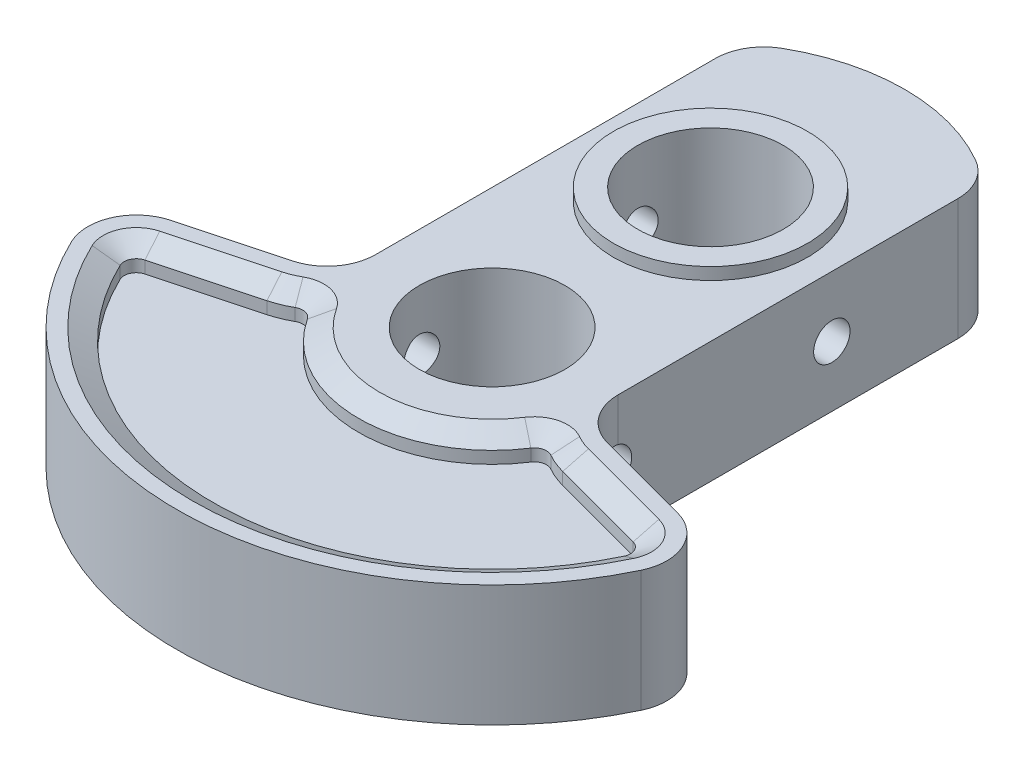
SolidWorks part; units mm, degrees
ref_plane "Front Plane" through (0, 0, 0) normal (0, 0, 1) x (1, 0, 0)
ref_plane "Top Plane" through (0, 0, 0) normal (0, 1, 0) x (1, 0, 0)
ref_plane "Right Plane" through (0, 0, 0) normal (1, 0, 0) x (0, 0, -1)
sketch "Sketch1" plane through (0, 0, 0) normal (0, 1, 0) x (1, 0, 0)
  line L0 (0, 34) -> (0, -26) construction
  line L1 (-10, 30.49) -> (-10, -2.6795)
  line L2 (10, 30.49) -> (10, -2.6795)
  line L3 (-10, 34) -> (-10, -40.4767) construction
  line L4 (10, 34) -> (10, -40.4767) construction
  line L5 (0, 0) -> (-25.1141, -6.7293) construction
  line L6 (0, 0) -> (25.1141, -6.7293) construction
  line L7 (0, 34) -> (0, -40.4767) construction
  line L8 (10, -2.6795) -> (25.1141, -6.7293)
  line L9 (-10, -2.6795) -> (-25.1141, -6.7293)
  arc A0 (10, 30.49) -> (-10, 30.49) centre (0, 18) ccw
  arc A2 (-25.1141, -6.7293) -> (25.1141, -6.7293) centre (0, 0) ccw
  dimension "D2" = 32
  dimension "D5" = 26
  dimension "D1" = 18
  dimension "D6" = 75
  dimension "D7" = 75
  dimension "D3" = 10
  dimension "D4" = 10
extrude "Boss-Extrude1" add sketch "Sketch1" along normal mid plane 10
fillet "Fillet1" radius 4 6 edges at (25.1141, 0, 6.7293) (10, 0, 2.6795) (-25.1141, 0, 6.7293) (-10, 0, 2.6795) (-10, 0, -30.49) (10, 0, -30.49)
sketch "Sketch2" plane through (0, -5, 0) normal (0, -1, 0) x (1, 0, 0)
  circle A0 centre (0, 0) radius 8
  dimension "D1" = 16
extrude "Boss-Extrude2" add sketch "Sketch2" along normal blind 1
sketch "Sketch3" plane through (0, 5, 0) normal (0, 1, 0) x (1, 0, 0)
  circle A0 centre (0, 18) radius 8
  dimension "D1" = 16
  dimension "D2" = 18
extrude "Boss-Extrude3" add sketch "Sketch3" along normal blind 1
sketch "Sketch4" plane through (0, -6, 0) normal (0, -1, 0) x (1, 0, 0)
  circle A0 centre (0, 0) radius 6
  circle A1 centre (0, -18) radius 6
  circle A3 centre (0, -18) radius 8 construction
  dimension "D1" = 12
  dimension "D2" = 12
extrude "Cut-Extrude1" cut sketch "Sketch4" against normal through all
sketch "Sketch5" plane through (0, 5, 0) normal (0, 1, 0) x (1, 0, 0)
  line L20 (12.1883, -6.3717) -> (20.1197, -8.4969)
  line L21 (-20.1197, -8.4969) -> (-12.1883, -6.3717)
  line L22 (12.1883, -6.3717) -> (20.1197, -8.4969)
  line L23 (-20.1197, -8.4969) -> (-12.1883, -6.3717)
  arc A1 (23.472, -11.1833) -> (20.8962, -5.5991) centre (19.8609, -9.4628) ccw construction
  arc A39 (-9.2082, -6.0173) -> (9.2082, -6.0173) centre (0, 0) ccw
  arc A40 (9.2082, -6.0173) -> (10.5397, -5.6951) centre (10.0453, -6.5644) cw
  arc A41 (-9.2082, -6.0173) -> (-10.5397, -5.6951) centre (-10.0453, -6.5644) ccw
  arc A44 (7, 0.3898) -> (12.1883, -6.3717) centre (14, 0.3898) ccw
  arc A45 (20.7637, -9.8929) -> (20.1197, -8.4969) centre (19.8609, -9.4628) ccw
  arc A46 (-20.7637, -9.8929) -> (20.7637, -9.8929) centre (0, 0) ccw
  arc A47 (-20.1197, -8.4969) -> (-20.7637, -9.8929) centre (-19.8609, -9.4628) ccw
  arc A48 (-12.1883, -6.3717) -> (-7, 0.3898) centre (-14, 0.3898) ccw
  arc A49 (10.5397, -5.6951) -> (12.1883, -6.3717) centre (14, 0.3898) ccw
  arc A50 (20.7637, -9.8929) -> (20.1197, -8.4969) centre (19.8609, -9.4628) ccw
  arc A51 (-20.7637, -9.8929) -> (20.7637, -9.8929) centre (0, 0) ccw
  arc A52 (-20.1197, -8.4969) -> (-20.7637, -9.8929) centre (-19.8609, -9.4628) ccw
  arc A53 (-12.1883, -6.3717) -> (-10.5397, -5.6951) centre (-14, 0.3898) ccw
  point P46 (23.4931, -7.7874)
  dimension "D2" = 22
  dimension "D3" = 1
  dimension "D1" = 3
extrude "Cut-Extrude2" cut sketch "Sketch5" against normal blind 2
chamfer "Chamfer1" distance 1 angle 60 10 edges at (11.3424, 5, 6.0861) (9.8101, 5, 5.5924) (16.154, 5, 7.4343) (0, 5, 11) (20.7689, 5, 9.044) (-9.8101, 5, 5.5924) (0, 5, 23) (-11.3424, 5, 6.0861) (-20.7689, 5, 9.044) (-16.154, 5, 7.4343)
mirror "Mirror3" about plane through (0, 0, 0) normal (0, 1, 0) of "Cut-Extrude2", "Chamfer1"
sketch "Sketch6" plane through (0, 0, 0) normal (1, 0, 0) x (0, 0, -1)
  circle A0 centre (0, 0) radius 1.5
  circle A1 centre (18, 0) radius 1.5
  dimension "D2" = 3
  dimension "D1" = 18
extrude "Cut-Extrude3" cut sketch "Sketch6" against normal through all both and the other way through all
